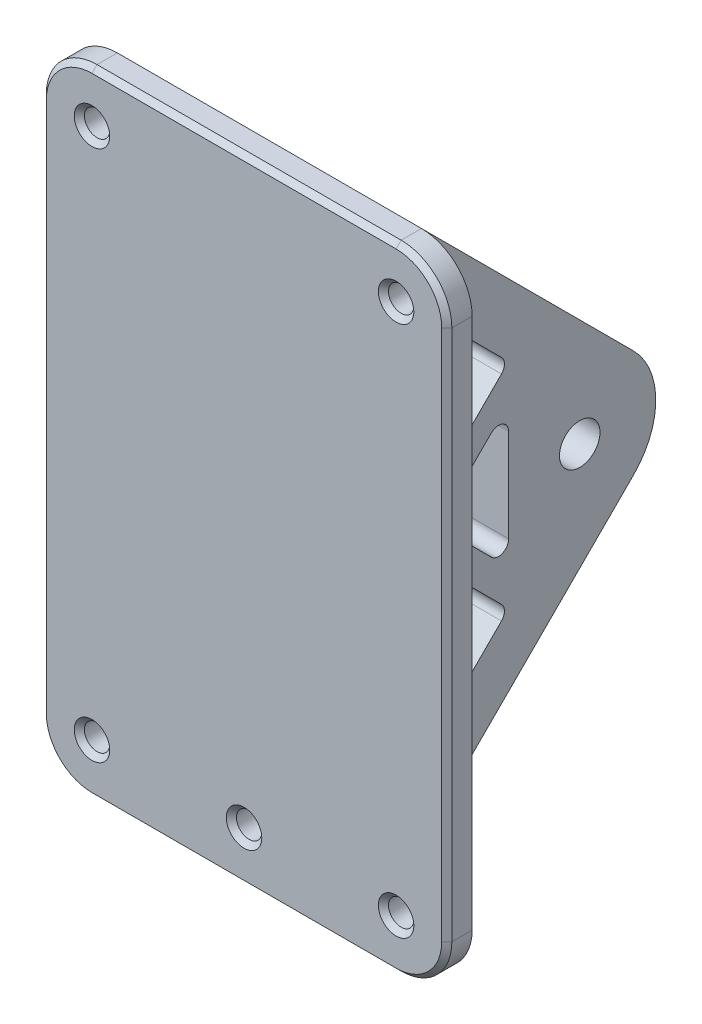
SolidWorks part; units mm, degrees
ref_plane "Plano frontal" through (0, 0, 0) normal (0, 0, 1) x (1, 0, 0)
ref_plane "Plano superior" through (0, 0, 0) normal (0, 1, 0) x (1, 0, 0)
ref_plane "Plano direito" through (0, 0, 0) normal (1, 0, 0) x (0, 0, -1)
ref_plane "Plano1" through (10, 0, 0) normal (1, 0, 0) x (0, 0, -1)
sketch "Esboço1" plane through (10, 0, 0) normal (1, 0, 0) x (0, 0, -1)
  line L0 (10, -24.1421) -> (10, -58.5537)
  line L1 (51.8397, -73.0529) -> (0, -124.8927)
  line L2 (0, -124.8927) -> (0, 0)
  line L3 (0, 0) -> (51.8397, -51.8397)
  line L4 (10, -100.7505) -> (27.2058, -83.5447)
  line L5 (10, -24.1421) -> (27.2058, -41.3479)
  line L6 (27.2058, -48.419) -> (27.2058, -76.4737)
  line L7 (27.2058, -83.5447) -> (10, -66.339)
  line L8 (27.2058, -76.4737) -> (13.1784, -62.4463)
  line L9 (27.2058, -41.3479) -> (10, -58.5537)
  line L10 (13.1784, -62.4463) -> (27.2058, -48.419)
  line L11 (10, -66.339) -> (10, -100.7505)
  circle A0 centre (41.2331, -62.4463) radius 4
  circle A1 centre (41.2331, -62.4463) radius 11 construction
  arc A2 (51.8397, -73.0529) -> (51.8397, -51.8397) centre (41.2331, -62.4463) ccw
  point P3 (0, -62.4463)
  point P12 (18.6029, -49.9508)
  dimension "D7" = 5
  dimension "D5" = 8
  dimension "D4" = 22
  dimension "D1" = 15
  dimension "D2" = 10
  dimension "D3" = 10
  dimension "D6" = 10
  dimension "D8" = 5
extrude "Ressalto-extrusão2" add sketch "Esboço1" along normal blind 10 contours A2 L3 L2 L1 | A2 A0
mirror "Espelhar2" about plane through (0, 0, 0) normal (1, 0, 0) of bodies 102
sketch "Esboço2" plane through (0, 0, 0) normal (0, 0, 1) x (1, 0, 0)
  line L1 (-40, 0) -> (40, 0)
  line L2 (-40, 0) -> (-40, -124.8927)
  line L3 (-40, -124.8927) -> (40, -124.8927)
  line L4 (40, 0) -> (40, -124.8927)
  line L5 (20, -124.8927) -> (10, -124.8927) construction
  line L8 (20, 0) -> (10, 0) construction
  line L9 (20, -124.8927) -> (20, 0) construction
  line L10 (-20, -124.8927) -> (-20, 0) construction
  circle A0 centre (-30, -10) radius 2.5
  circle A1 centre (30, -10) radius 2.5
  circle A2 centre (-30, -114.8927) radius 2.5
  circle A3 centre (30, -114.8927) radius 2.5
  circle A4 centre (0, -114.8927) radius 2.5
  point P22 (0, 0)
  point P23 (0, 0)
  point P24 (0, 0)
  dimension "D3" = 5
  dimension "D6" = 5
  dimension "D11" = 5
  dimension "D7" = 5
  dimension "D10" = 5
  dimension "D4" = 10
  dimension "D8" = 10
  dimension "D9" = 10
  dimension "D12" = 20
  dimension "D2" = 20
  dimension "D5" = 10
extrude "Ressalto-extrusão3" add sketch "Esboço2" along normal blind 5
fillet "Filete5" radius 2 9 edges at (15, -83.5447, -27.2058) (15, -66.339, -10) (15, -100.7505, -10) (15, -76.4737, -27.2058) (15, -58.5537, -10) (15, -48.419, -27.2058) (15, -41.3479, -27.2058) (15, -24.1421, -10) (15, -62.4463, -13.1784)
fillet "Filete6" radius 5 4 edges at (-10, -62.4463, 0) (-20, -62.4463, 0) (10, -62.4463, 0) (20, -62.4463, 0)
fillet "Filete7" radius 10 4 edges at (-40, -124.8927, 2.5) (40, -124.8927, 2.5) (-40, 0, 2.5) (40, 0, 2.5)
chamfer "Chanfro1" distance 1 angle 45 13 edges at (2.5, -114.8927, 5) (-27.5, -10, 5) (-37.0711, -2.9289, 5) (0, 0, 5) (37.0711, -2.9289, 5) (40, -62.4463, 5) (37.0711, -121.9637, 5) (0, -124.8927, 5) (-37.0711, -121.9637, 5) (-40, -62.4463, 5) (32.5, -10, 5) (-27.5, -114.8927, 5) (32.5, -114.8927, 5)
equation "\"D6@Esboço2\"=\"D3@Esboço2\""
equation "\"D11@Esboço2\"=\"D3@Esboço2\""
equation "\"D2@Esboço2\"=\"D12@Esboço2\""
equation "\"D8@Esboço1\"=\"D7@Esboço1\""
equation "\"D2@Esboço1\"=\"D3@Esboço1\""
equation "\"D6@Esboço1\"=\"D3@Esboço1\""
equation "\"D7@Esboço2\"=\"D3@Esboço2\""
equation "\"D10@Esboço2\"=\"D3@Esboço2\""
